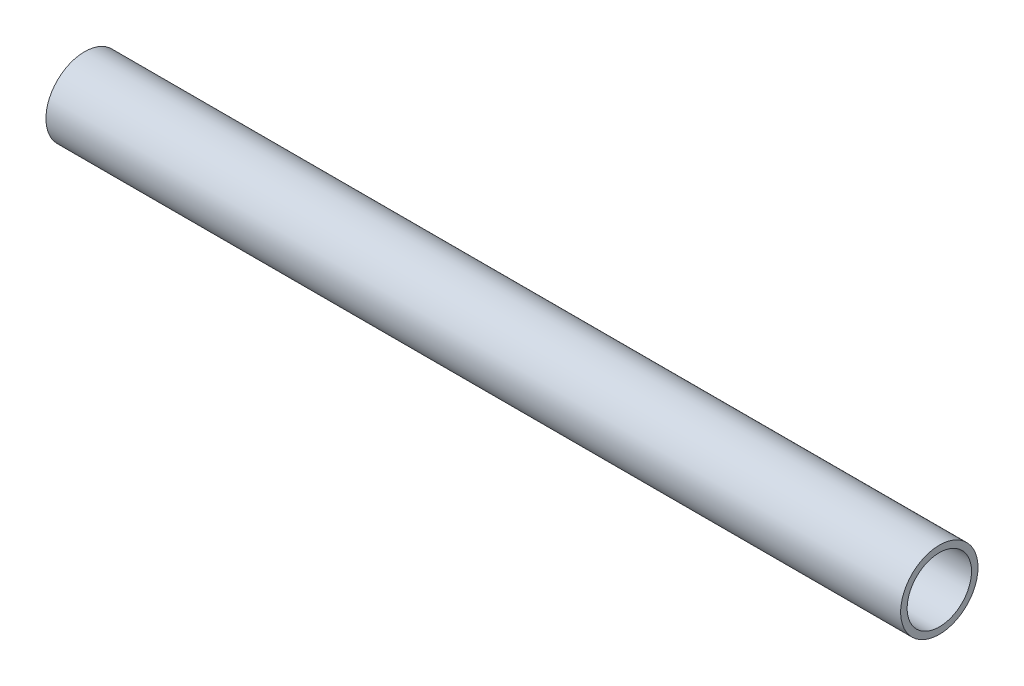
SolidWorks part; units mm, degrees
ref_plane "Front Plane" through (0, 0, 0) normal (0, 0, 1) x (1, 0, 0)
ref_plane "Top Plane" through (0, 0, 0) normal (0, 1, 0) x (1, 0, 0)
ref_plane "Right Plane" through (0, 0, 0) normal (1, 0, 0) x (0, 0, -1)
sketch "Sketch1" plane through (0, 0, 0) normal (0, 0, 1) x (1, 0, 0)
  line L0 (-106.534, 1471.8597) -> (33.8327, 1471.8597)
  point P2 (31.8812, 1471.8597)
  point P3 (33.8327, 1471.8597)
other "Pipe 0.5 SCH 40(1)"
ref_plane "Plane1" through (-106.534, 1471.8597, 0) normal (1, 0, 0) x (0, 1, 0)
sketch "Sketch11" plane through (-106.534, 1471.8597, 0) normal (1, 0, 0) x (0, 1, 0)
  circle A0 centre (0, 0) radius 5.2832
  circle A1 centre (0, 0) radius 6.35
  point P5 (0, 0)
  dimension "D1" = 12.7
  dimension "D2" = 10.5664
